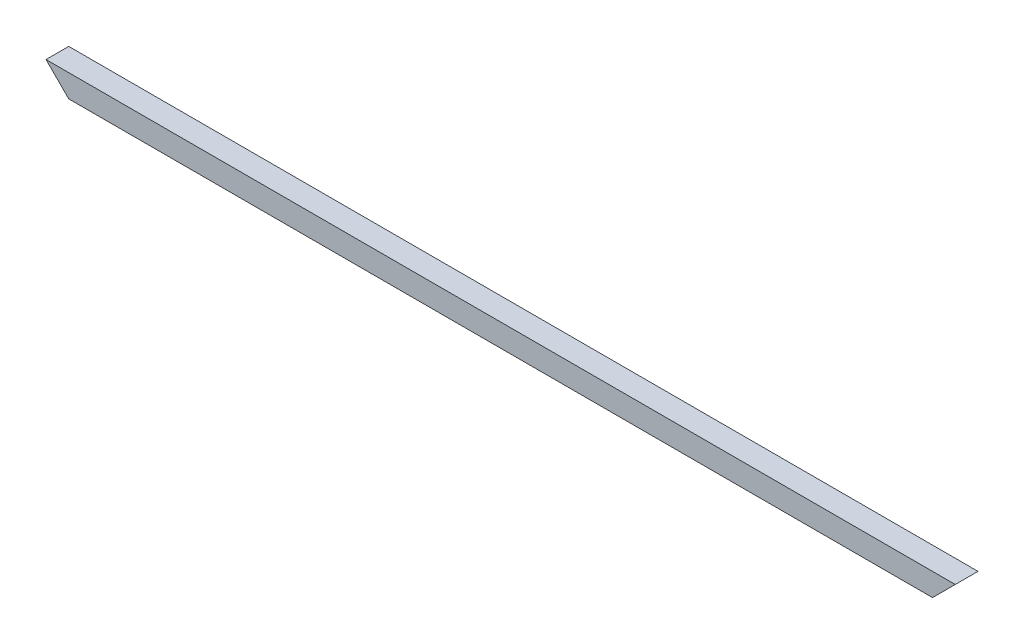
SolidWorks part; units mm, degrees
material "Stainless Steel (ferritic)"
ref_plane "Front Plane" through (0, 0, 0) normal (0, 0, 1) x (1, 0, 0)
ref_plane "Top Plane" through (0, 0, 0) normal (0, 1, 0) x (1, 0, 0)
ref_plane "Right Plane" through (0, 0, 0) normal (1, 0, 0) x (0, 0, -1)
sketch "Sketch1" plane through (0, 0, 0) normal (1, 0, 0) x (0, 0, -1)
  line L0 (-8.8, 8.8) -> (8.8, 8.8)
  line L1 (-10, -10) -> (10, -10)
  line L2 (-10, -10) -> (-10, 10)
  line L3 (-10, 10) -> (10, 10)
  line L4 (10, -10) -> (10, 10)
  line L5 (-10, -10) -> (10, 10) construction
  line L6 (-10, 10) -> (10, -10) construction
  line L7 (8.8, -8.8) -> (8.8, 8.8)
  line L8 (-8.8, -8.8) -> (8.8, -8.8)
  line L9 (-8.8, -8.8) -> (-8.8, 8.8)
  point P0 (0, 0)
  dimension "D1" = 20
  dimension "D2" = 20
  dimension "D3" = 1.2
extrude "Boss-Extrude1" add sketch "Sketch1" along normal blind 800
sketch "Sketch2" plane through (0, 0, 10) normal (0, 0, 1) x (1, 0, 0)
  line L0 (0, 10) -> (20, -10)
  line L1 (800, -10) -> (0, -10) construction
  line L2 (0, 10) -> (0, -10) construction
  dimension "D1" = 45
extrude "Cut-Extrude1" cut sketch "Sketch2" against normal through all and the other way through all flip side to cut
sketch "Sketch3" plane through (0, 0, 10) normal (0, 0, 1) x (1, 0, 0)
  line L0 (800, 10) -> (780, -10)
  line L1 (800, -10) -> (20, -10) construction
  line L2 (800, 10) -> (800, -10) construction
  dimension "D1" = 45
extrude "Cut-Extrude2" cut sketch "Sketch3" against normal through all and the other way through all
